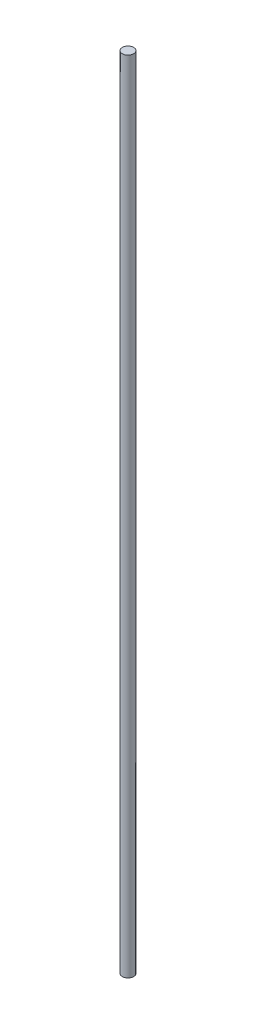
SolidWorks part; units mm, degrees
material "Chrome Stainless Steel"
ref_plane "Front Plane" through (0, 0, 0) normal (0, 0, 1) x (1, 0, 0)
ref_plane "Top Plane" through (0, 0, 0) normal (0, 1, 0) x (1, 0, 0)
ref_plane "Right Plane" through (0, 0, 0) normal (1, 0, 0) x (0, 0, -1)
sketch "Sketch1" plane through (0, 0, 0) normal (0, 1, 0) x (1, 0, 0)
  circle A0 centre (0, 0) radius 4
  dimension "D1" = 8
extrude "Boss-Extrude1" add sketch "Sketch1" along normal blind 570 contours A0
